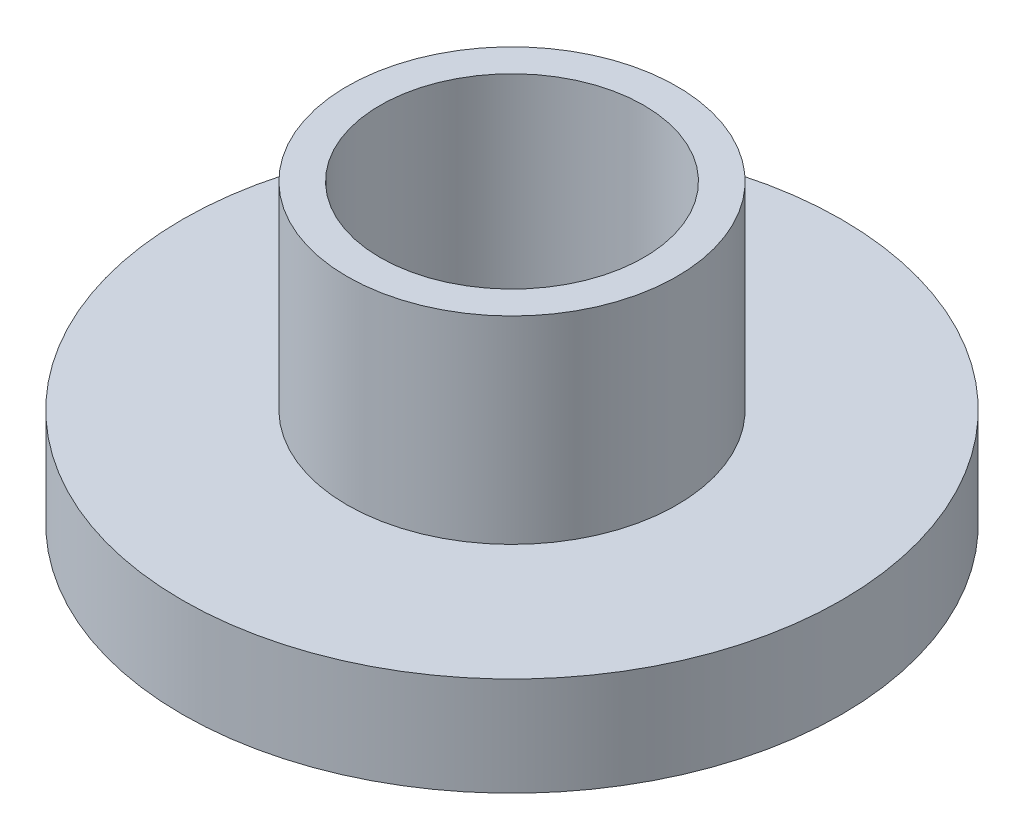
SolidWorks part; units mm, degrees
ref_plane "前视基准面" through (0, 0, 0) normal (0, 0, 1) x (1, 0, 0)
ref_plane "上视基准面" through (0, 0, 0) normal (0, 1, 0) x (1, 0, 0)
ref_plane "右视基准面" through (0, 0, 0) normal (1, 0, 0) x (0, 0, -1)
sketch "草图1" plane through (0, 0, 0) normal (0, 1, 0) x (1, 0, 0)
  circle A0 centre (0, 0) radius 5
  circle A1 centre (0, 0) radius 2
  dimension "D1" = 4
  dimension "D2" = 10
extrude "凸台-拉伸1" add sketch "草图1" along normal blind 1.5
sketch "草图2" plane through (0, 1.5, 0) normal (0, 1, 0) x (1, 0, 0)
  circle A0 centre (0, 0) radius 2 construction
  circle A1 centre (0, 0) radius 2
  circle A2 centre (0, 0) radius 2.5
  dimension "D1" = 5
extrude "凸台-拉伸2" add sketch "草图2" along normal blind 3
